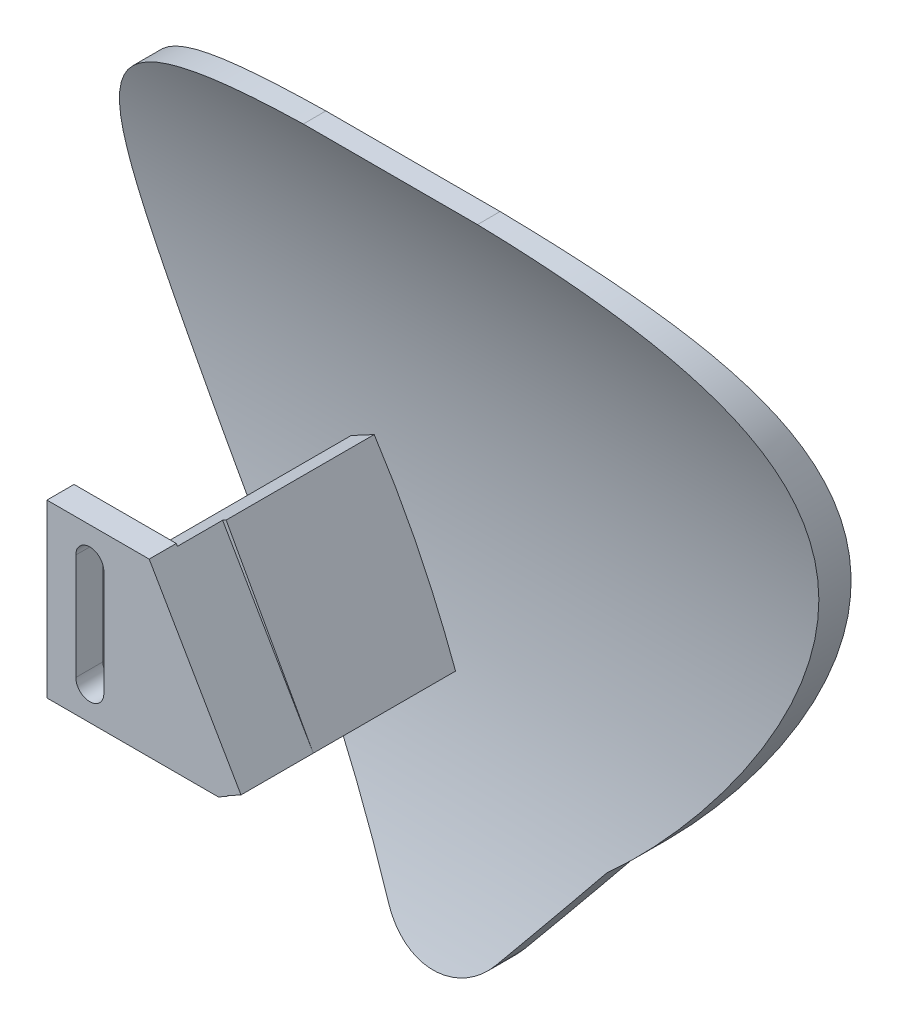
SolidWorks part; units mm, degrees
ref_plane "Front Plane" through (0, 0, 0) normal (0, 0, 1) x (1, 0, 0)
ref_plane "Top Plane" through (0, 0, 0) normal (0, 1, 0) x (1, 0, 0)
ref_plane "Right Plane" through (0, 0, 0) normal (1, 0, 0) x (0, 0, -1)
sketch "Sketch1" plane through (0, 0, 0) normal (0, 0, 1) x (1, 0, 0)
  line L1 (-45, 45) -> (45, 45)
  line L2 (-45, 45) -> (-45, -45)
  line L3 (-45, -45) -> (45, -45)
  line L4 (45, 45) -> (45, -45)
  line L5 (-45, 45) -> (45, -45) construction
  line L6 (-45, -45) -> (45, 45) construction
  point P0 (0, 0)
  dimension "D1" = 90
  dimension "D2" = 90
extrude "Boss-Extrude1" add sketch "Sketch1" along normal blind 20
sketch "Sketch2" plane through (0, 0, 0) normal (1, 0, 0) x (0, 0, -1)
  line L0 (-20, 45) -> (0, 45) construction
  line L1 (-20, -45) -> (0, -45) construction
  line L3 (4.0597, 48.8234) -> (-32.6929, 48.8234)
  line L4 (4.0597, 48.8234) -> (4.0597, -49.8938)
  line L5 (4.0597, -49.8938) -> (-32.6929, -49.8938)
  line L6 (-32.6929, 48.8234) -> (-32.6929, -49.8938)
  line L7 (0, 45) -> (-20, 45)
  line L8 (0, 45) -> (0, -45)
  line L9 (0, -45) -> (-20, -45)
  line L10 (-20, 45) -> (-20, -45)
  spline S0 degree 2 poles (-20, 45) (3.101, 4.7541) (-20, -45) knots 0 0 0 1 1 1
  spline S1 degree 3 poles (-17.5, 45) (1.1153, 18.3301) (-2.773, -17.8121) (-17.5, -45) knots 0 0 0 0 1 1 1 1
  dimension "D1" = 2.5
  dimension "D2" = 2.5
extrude "Cut-Extrude1" cut sketch "Sketch2" against normal through all both and the other way through all contours L7 S1 L9 L8 | S0 L10
sketch "Sketch3" plane through (0, 0, 0) normal (0, 0, 1) x (1, 0, 0)
  line L0 (0, -51.9556) -> (0, 51.9556) construction
  line L1 (-5.9529, -30.6816) -> (-23.8117, -7.3781)
  line L2 (5.9529, -30.6816) -> (23.8117, -7.3781)
  line L4 (45, 45) -> (-45, 45)
  line L5 (45, 45) -> (45, -45)
  line L6 (45, -45) -> (-45, -45)
  line L7 (-45, 45) -> (-45, -45)
  circle A0 centre (0, -26.1195) radius 7.5
  circle A1 centre (0, 10.8702) radius 30
  spline S0 degree 3 poles (14.8823, -19.0298) (34.5015, -1.8338) (60.9654, 47.9262) (0, 45) knots 0 0 0 0 1 1 1 1
  spline S1 degree 3 poles (-14.8823, -19.0298) (-34.5015, -1.8338) (-60.9654, 47.9262) (0, 45) knots 0 0 0 0 1 1 1 1
  point P4 (0, 0)
  dimension "D1" = 15
  dimension "D2" = 60
extrude "Cut-Extrude2" cut sketch "Sketch3" against normal through all both and the other way through all contours L6 L0 A0 L1 A1 L4 L7 | L0 L6 L5 L4 A1 L2 A0
sketch "Sketch15" plane through (0, 0, 0) normal (1, 0, 0) x (0, 0, -1)
  line L0 (-6.5443, -14.084) -> (-5.9164, -10.262)
  line L1 (-5.9164, -10.262) -> (-5.1854, -14.084)
  line L2 (-5.1854, -14.084) -> (-6.5443, -14.084)
  spline S0 degree 3 poles (-17.5, 45) (-4.3851, 26.2105) (-2.4399, 2.7193) (-7.5853, -19.0298) knots 0 0 0 0 0.704523 0.704523 0.704523 0.704523 construction
extrude "Cut-Extrude13" cut sketch "Sketch15" along normal blind 10
sketch "Sketch24" plane through (0, 0, 0) normal (0, 0, 1) x (1, 0, 0)
  line L0 (-15.8028, 6.3361) -> (-6.1559, -11.1835)
  line L1 (-6.1559, -11.1835) -> (-3.528, -9.7365)
  line L2 (-3.528, -9.7365) -> (-13.1748, 7.7832)
  line L3 (-13.1748, 7.7832) -> (-15.8028, 6.3361)
  dimension "D1" = 3
  dimension "D2" = 3
  dimension "D3" = 20
extrude "Boss-Extrude5" add sketch "Sketch24" along normal blind 26.5 from offset 6.5
sketch "Sketch26" plane through (0, 0, 0) normal (1, 0, 0) x (0, 0, -1)
  line L0 (-33, 7.7832) -> (-8.6184, 7.7832) construction
  line L1 (-33, -11.1835) -> (-30, -11.1835)
  line L2 (-33, -11.1835) -> (-33, 7.7832)
  line L3 (-33, 7.7832) -> (-30, 7.7832)
  line L4 (-30, -11.1835) -> (-30, 7.7832)
  dimension "D1" = 3
extrude "Boss-Extrude7" add sketch "Sketch26" along normal blind 20 from offset 25 offset against normal yes
sketch "Sketch28" plane through (0, 0, 0) normal (0, 0, 1) x (1, 0, 0)
  line L0 (-18.7068, 4.1151) -> (-18.7068, -7.6193)
  line L1 (-21.8068, 4.1151) -> (-21.8068, -7.6193)
  circle A0 centre (-20.2568, 4.1151) radius 1.55
  circle A1 centre (-20.2568, -7.6193) radius 1.55
  dimension "D1" = 3.1
  dimension "D2" = 3.1
extrude "Cut-Extrude23" cut sketch "Sketch28" along normal blind 10 from offset 25 contours A0 | A1 L0 A0 L1 | A1
sketch "Sketch29" plane through (0, 0, 0) normal (0, 0, 1) x (1, 0, 0)
  line L0 (-3.528, -9.7365) -> (-13.6884, 7.7832)
  line L1 (-5, 7.7832) -> (-25, 7.7832) construction
  line L2 (-13.6884, 7.7832) -> (-3.7762, 7.7832)
  line L3 (-3.7762, 7.7832) -> (-3.528, -9.7365)
  line L4 (-3.528, -9.7365) -> (-7.3567, -11.957)
  line L5 (-7.3567, -11.957) -> (-3.6521, -11.957)
  line L6 (-3.6521, -11.957) -> (-3.528, -9.7365)
extrude "Cut-Extrude24" cut sketch "Sketch29" against normal blind 10 from offset 35 contours L3 L2 L0 | L5 L6 L4
